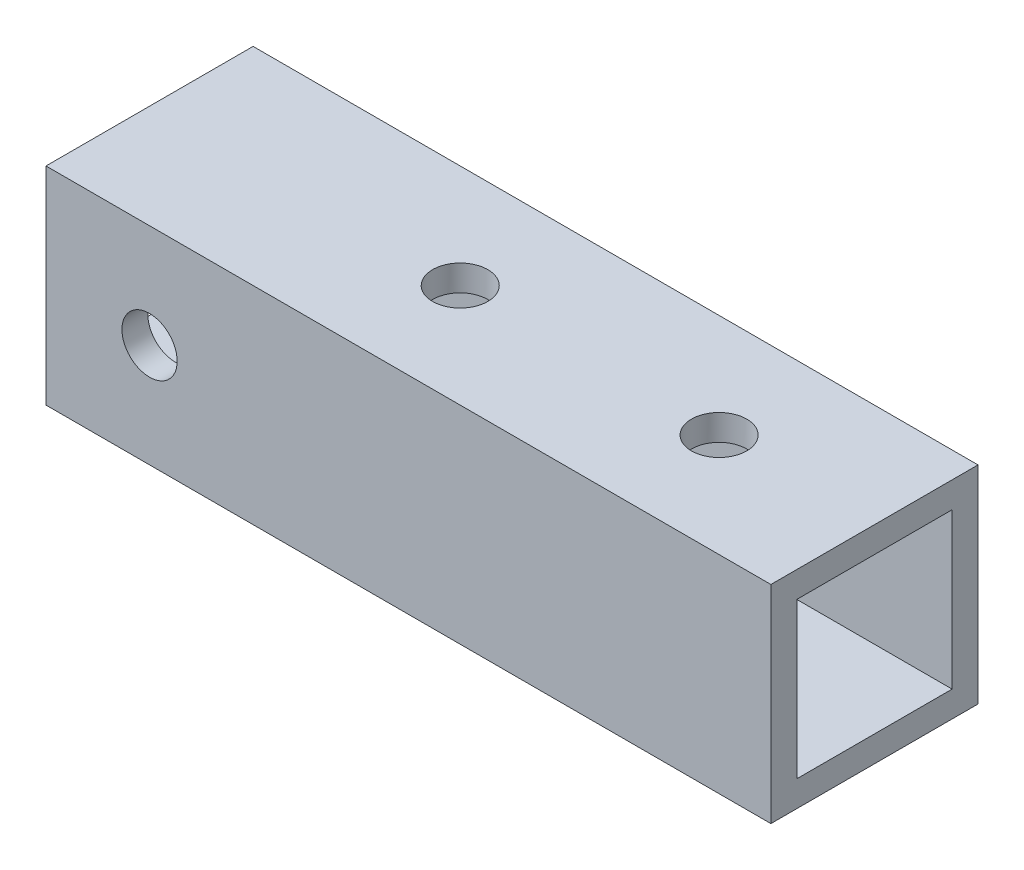
SolidWorks part; units mm, degrees
material "5052-O"
ref_plane "正面" through (0, 0, 0) normal (0, 0, 1) x (1, 0, 0)
ref_plane "平面" through (0, 0, 0) normal (0, 1, 0) x (1, 0, 0)
ref_plane "右側面" through (0, 0, 0) normal (1, 0, 0) x (0, 0, -1)
sketch "ｽｹｯﾁ1" plane through (0, 0, 0) normal (1, 0, 0) x (0, 0, -1)
  line L0 (4.5, 4.5) -> (4.5, -4.5)
  line L1 (6, 6) -> (-6, 6)
  line L2 (6, 6) -> (6, -6)
  line L3 (6, -6) -> (-6, -6)
  line L4 (-6, 6) -> (-6, -6)
  line L5 (6, 6) -> (-6, -6) construction
  line L6 (6, -6) -> (-6, 6) construction
  line L7 (4.5, -4.5) -> (-4.5, -4.5)
  line L8 (-4.5, 4.5) -> (-4.5, -4.5)
  line L9 (4.5, 4.5) -> (-4.5, 4.5)
  point P0 (0, 0)
  dimension "D1" = 12
  dimension "D2" = 12
  dimension "D3" = 1.5
extrude "ﾎﾞｽ - 押し出し1" add sketch "ｽｹｯﾁ1" along normal mid plane 42
sketch "ｽｹｯﾁ4" plane through (0, 6, 0) normal (0, 1, 0) x (1, 0, 0)
  line L0 (-21, 0) -> (21, 0) construction
  line L1 (-21, -6) -> (-21, 6) construction
  line L2 (21, -6) -> (21, 6) construction
  line L3 (0, -6) -> (0, 6) construction
  line L4 (21, -6) -> (-21, -6) construction
  line L5 (21, 6) -> (-21, 6) construction
  line L6 (21, 6) -> (21, -6) construction
  line L7 (-21, 6) -> (-21, -6) construction
  circle A0 centre (-3, 0) radius 1.6
  circle A1 centre (12, 0) radius 1.6
  dimension "D1" = 3.2
  dimension "D2" = 9
  dimension "D3" = 18
extrude "ｶｯﾄ - 押し出し3" cut sketch "ｽｹｯﾁ4" against normal through all
sketch "ｽｹｯﾁ5" plane through (0, 0, 6) normal (0, 0, 1) x (1, 0, 0)
  line L0 (-21, 0) -> (21, 0) construction
  line L1 (-21, 6) -> (-21, -6) construction
  line L2 (21, 6) -> (21, -6) construction
  line L3 (0, 6) -> (0, -6) construction
  line L4 (21, 6) -> (-21, 6) construction
  line L5 (21, -6) -> (-21, -6) construction
  circle A0 centre (-15, 0) radius 1.6
  dimension "D1" = 3.2
  dimension "D3" = 6
extrude "ｶｯﾄ - 押し出し4" cut sketch "ｽｹｯﾁ5" against normal through all
